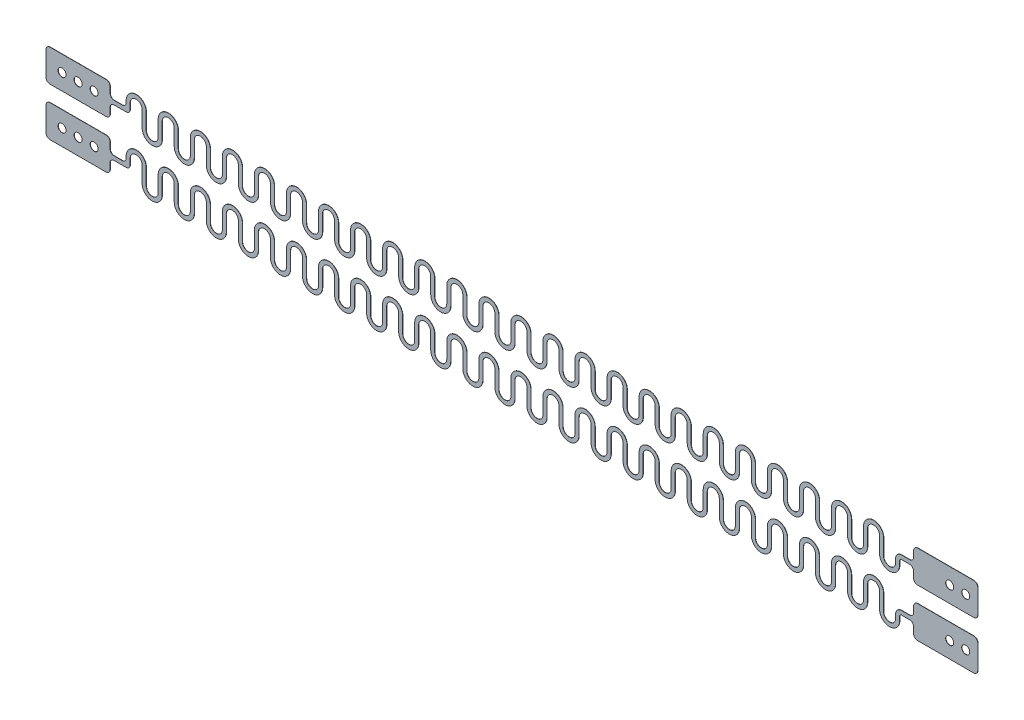
SolidWorks part; units mm, degrees
material "Copper"
ref_plane "Front Plane" through (0, 0, 0) normal (0, 0, 1) x (1, 0, 0)
ref_plane "Top Plane" through (0, 0, 0) normal (0, 1, 0) x (1, 0, 0)
ref_plane "Right Plane" through (0, 0, 0) normal (1, 0, 0) x (0, 0, -1)
sketch "Sketch1" plane through (0, 0, 0) normal (0, 0, 1) x (1, 0, 0)
  line L0 (0, -1.5) -> (0, 1.5) construction
  line L2 (-2, 0.5) -> (2, 0.5)
  line L3 (-2, 0.5) -> (-2, 2.5)
  line L4 (-2, 2.5) -> (2, 2.5)
  line L5 (2, 0.5) -> (2, 2.5)
  line L6 (-2, 0.5) -> (2, 2.5) construction
  line L7 (-2, 2.5) -> (2, 0.5) construction
  line L8 (-2, -2.5) -> (2, -2.5)
  line L9 (-2, -2.5) -> (-2, -0.5)
  line L10 (-2, -0.5) -> (2, -0.5)
  line L11 (2, -2.5) -> (2, -0.5)
  line L12 (-2, -2.5) -> (2, -0.5) construction
  line L13 (-2, -0.5) -> (2, -2.5) construction
  point P4 (0, 0)
  dimension "D1" = 2
  dimension "D2" = 4
  dimension "D3" = 2
  dimension "D5" = 3
  dimension "D12" = 4
extrude "Boss-Extrude2" add sketch "Sketch1" along normal blind 0.015
sketch "Sketch4" plane through (0, 0, 0) normal (0, 0, 1) x (1, 0, 0)
  line L0 (-2, -1.5) -> (-2.75, -1.5) construction
  line L2 (-3, -1.75) -> (-3, -2) construction
  line L3 (-3, -2) -> (-4, -2) construction
  line L4 (-4, -2) -> (-4, -1) construction
  line L5 (-4, -1) -> (-5, -1) construction
  line L22 (-5, -1) -> (-5, -1.5) construction
  line L23 (-2, -0.5) -> (-2, -2.5) construction
  line L24 (-2, -0.5) -> (-2, -2.5)
  line L25 (-2, -1.375) -> (-2.75, -1.375)
  line L30 (-3.125, -1.75) -> (-3.125, -2)
  line L31 (-3.875, -2) -> (-3.875, -1)
  line L32 (-5.125, -1) -> (-5.125, -1.5)
  line L33 (-2, -1.625) -> (-2.75, -1.625)
  line L34 (-2.875, -1.75) -> (-2.875, -2)
  line L35 (-4.125, -2) -> (-4.125, -1)
  line L36 (-4.875, -1) -> (-4.875, -1.5)
  line L37 (-5.125, -1.5) -> (-4.875, -1.5)
  arc A0 (-2.75, -1.5) -> (-3, -1.75) centre (-2.75, -1.75) ccw construction
  arc A1 (-5, -1) -> (-4, -1) centre (-4.5, -1) cw construction
  arc A2 (-4, -2) -> (-3, -2) centre (-3.5, -2) ccw construction
  arc A15 (-2.75, -1.375) -> (-3.125, -1.75) centre (-2.75, -1.75) ccw
  arc A16 (-3.875, -2) -> (-3.125, -2) centre (-3.5, -2) ccw
  arc A17 (-5.125, -1) -> (-3.875, -1) centre (-4.5, -1) cw
  arc A18 (-2.75, -1.625) -> (-2.875, -1.75) centre (-2.75, -1.75) ccw
  arc A19 (-4.125, -2) -> (-2.875, -2) centre (-3.5, -2) ccw
  arc A20 (-4.875, -1) -> (-4.125, -1) centre (-4.5, -1) cw
  point P9 (-3, -1.5)
  dimension "D5" = 1
  dimension "D7" = 0.25
  dimension "D8" = 0.5
  dimension "D9" = 0.5
  dimension "D1" = 1
  dimension "D2" = 0.5
  dimension "D3" = 1
  dimension "D4" = 1
  dimension "D6" = 0.5
  dimension "D11" = 0.125
  dimension "D10" = 0.125
extrude "Boss-Extrude4" add sketch "Sketch4" along normal blind 0.015
fillet "Fillet1" radius 0.25 6 edges at (-2, -0.5, 0.0075) (2, -0.5, 0.0075) (2, -2.5, 0.0075) (-2, -2.5, 0.0075) (-2, -1.375, 0.0075) (-2, -1.625, 0.0075)
sketch "Sketch5" plane through (0, 0, 0.015) normal (0, 0, 1) x (1, 0, 0)
  line L0 (2, -1.5) -> (1.25, -1.5) construction
  line L1 (2, -2.25) -> (2, -0.75) construction
  circle A0 centre (1.25, -1.5) radius 0.25
  circle A1 centre (0.25, -1.5) radius 0.25
  dimension "D2" = 0.5
  dimension "D1" = 0.75
  dimension "D3" = 2
extrude "Cut-Extrude1" cut sketch "Sketch5" against normal through all
sketch "Sketch7" plane through (0, 0, 0) normal (0, 0, 1) x (1, 0, 0)
  line L0 (-2, -1.5) -> (-2.75, -1.5) construction
  line L1 (-5, 2) -> (-5, 1.5)
  line L2 (-3, -1.75) -> (-3, -2) construction
  line L3 (-3, -2) -> (-4, -2) construction
  line L4 (-4, -2) -> (-4, -1) construction
  line L5 (-4, -1) -> (-5, -1) construction
  line L6 (-4.125, -2) -> (-4.125, -1)
  line L7 (-2.875, -1.75) -> (-2.875, -2)
  line L8 (-2, -1.625) -> (-2.75, -1.625)
  line L9 (-3.875, -2) -> (-3.875, -1)
  line L10 (-3.125, -1.75) -> (-3.125, -2)
  line L11 (-2, -1.375) -> (-2.75, -1.375)
  line L13 (-2, -1.625) -> (-2, -1.375)
  line L14 (-4.125, 1) -> (-4.125, 2)
  line L15 (-2.875, 1.25) -> (-2.875, 1)
  line L16 (-2, 1.375) -> (-2.75, 1.375)
  line L17 (-3.875, 1) -> (-3.875, 2)
  line L18 (-3.125, 1.25) -> (-3.125, 1)
  line L19 (-2, 1.625) -> (-2.75, 1.625)
  line L20 (-5.125, 2) -> (-4.875, 2)
  line L21 (-2, 1.5) -> (-2.75, 1.5) construction
  line L22 (-3, 1.25) -> (-3, 1) construction
  line L23 (-3, 1) -> (-4, 1) construction
  line L24 (-4, 1) -> (-4, 2) construction
  line L25 (-4, 2) -> (-5, 2) construction
  line L26 (-5.125, -1) -> (-5.125, -1.5)
  line L27 (-5.125, -1.5) -> (-4.875, -1.5)
  line L28 (-4.875, -1.5) -> (-4.875, -1)
  line L29 (-2, 1.375) -> (-2, 1.625)
  line L30 (-5, 1.5) -> (-4.875, 1.5)
  line L31 (-4.875, 1.5) -> (-4.875, 2)
  line L32 (-5.125, 2) -> (-5.125, 1.5)
  line L33 (-5.125, 1.5) -> (-5, 1.5)
  arc A0 (-3, -2) -> (-4, -2) centre (-3.5, -2) cw construction
  arc A1 (-5, -1) -> (-4, -1) centre (-4.5, -1) cw construction
  arc A2 (-2.75, -1.5) -> (-3, -1.75) centre (-2.75, -1.75) ccw construction
  arc A3 (-4.875, -1) -> (-4.125, -1) centre (-4.5, -1) cw
  arc A4 (-2.875, -2) -> (-4.125, -2) centre (-3.5, -2) cw
  arc A5 (-2.75, -1.625) -> (-2.875, -1.75) centre (-2.75, -1.75) ccw
  arc A6 (-5.125, -1) -> (-3.875, -1) centre (-4.5, -1) cw
  arc A7 (-3.125, -2) -> (-3.875, -2) centre (-3.5, -2) cw
  arc A8 (-2.75, -1.375) -> (-3.125, -1.75) centre (-2.75, -1.75) ccw
  arc A9 (-4.875, 2) -> (-4.125, 2) centre (-4.5, 2) cw
  arc A10 (-2.875, 1) -> (-4.125, 1) centre (-3.5, 1) cw
  arc A11 (-2.75, 1.375) -> (-2.875, 1.25) centre (-2.75, 1.25) ccw
  arc A12 (-5.125, 2) -> (-3.875, 2) centre (-4.5, 2) cw
  arc A13 (-3.125, 1) -> (-3.875, 1) centre (-3.5, 1) cw
  arc A14 (-2.75, 1.625) -> (-3.125, 1.25) centre (-2.75, 1.25) ccw
  arc A15 (-3, 1) -> (-4, 1) centre (-3.5, 1) cw construction
  arc A16 (-5, 2) -> (-4, 2) centre (-4.5, 2) cw construction
  arc A17 (-2.75, 1.5) -> (-3, 1.25) centre (-2.75, 1.25) ccw construction
  point P13 (-3, -1.5)
  dimension "D5" = 0.5
  dimension "D7" = 0.5
  dimension "D8" = 0.25
  dimension "D1" = 1
  dimension "D2" = 0.5
  dimension "D3" = 1
  dimension "D4" = 1
  dimension "D6" = 1
  dimension "D11" = 2
  dimension "D12" = 0.5
  dimension "D9" = 0.125
  dimension "D10" = 0.125
extrude "Boss-Extrude9" add sketch "Sketch7" along normal blind 0.015 contours L19 A14 L18 A13 L17 A12 L20 A9 L14 A10 L15 A11 L16 L29 | L32 L33 L1 L20 | L30 L31 L20 L1
fillet "Fillet2" radius 0.25 6 edges at (2, 2.5, 0.0075) (-2, 1.625, 0.0075) (-2, 2.5, 0.0075) (2, 0.5, 0.0075) (-2, 0.5, 0.0075) (-2, 1.375, 0.0075)
sketch "Sketch8" plane through (0, 0, 0.015) normal (0, 0, 1) x (1, 0, 0)
  line L0 (2, 1.5) -> (1.25, 1.5) construction
  line L1 (2, 0.75) -> (2, 2.25) construction
  circle A0 centre (1.25, 1.5) radius 0.25
  circle A1 centre (0.25, 1.5) radius 0.25
  dimension "D2" = 0.5
  dimension "D1" = 0.75
  dimension "D3" = 2
extrude "Cut-Extrude2" cut sketch "Sketch8" against normal through all
sketch "Sketch9" plane through (0, 0, 0) normal (0, 0, 1) x (1, 0, 0)
  line L2 (-5, -1.5) -> (-5, -2) construction
  line L3 (-5, -2) -> (-6, -2) construction
  line L4 (-6, -2) -> (-6, -1) construction
  line L5 (-6, -1) -> (-7, -1) construction
  line L6 (-7, -1) -> (-7, -1.5) construction
  line L7 (-5.125, -1.5) -> (-5.125, -2)
  line L8 (-5.875, -2) -> (-5.875, -1)
  line L9 (-7.125, -1) -> (-7.125, -1.5)
  line L10 (-4.875, -1.5) -> (-4.875, -2)
  line L11 (-6.125, -2) -> (-6.125, -1)
  line L12 (-6.875, -1) -> (-6.875, -1.5)
  line L13 (-7.125, -1.5) -> (-6.875, -1.5)
  line L14 (-5.125, -1.5) -> (-4.875, -1.5) construction
  line L15 (-5.125, -1.5) -> (-4.875, -1.5)
  arc A0 (-5, -2) -> (-6, -2) centre (-5.5, -2) cw construction
  arc A1 (-6, -1) -> (-7, -1) centre (-6.5, -1) ccw construction
  arc A2 (-5.125, -2) -> (-5.875, -2) centre (-5.5, -2) cw
  arc A3 (-5.875, -1) -> (-7.125, -1) centre (-6.5, -1) ccw
  arc A4 (-4.875, -2) -> (-6.125, -2) centre (-5.5, -2) cw
  arc A5 (-6.125, -1) -> (-6.875, -1) centre (-6.5, -1) ccw
  dimension "D6" = 0.5
  dimension "D7" = 0.5
  dimension "D1" = 0.5
  dimension "D2" = 1
  dimension "D3" = 1
  dimension "D4" = 1
  dimension "D5" = 0.5
  dimension "D8" = 0.125
  dimension "D9" = 0.125
extrude "Boss-Extrude10" add sketch "Sketch9" along normal up to surface (0.015 mm away) up to face at (1.5, -1.5, 0.015)
sketch "Sketch14" plane through (0, 0, 0.015) normal (0, 0, 1) x (1, 0, 0)
  line L0 (-5.125, 1.5) -> (-4.875, 1.5) construction
  line L1 (-5.125, 1.5) -> (-4.875, 1.5)
  line L2 (-5, 1.5) -> (-5, 1) construction
  line L3 (-5, 1) -> (-6, 1) construction
  line L4 (-6, 1) -> (-6, 2) construction
  line L5 (-6, 2) -> (-7, 2) construction
  line L6 (-7, 2) -> (-7, 1.5) construction
  line L7 (-5.125, 1.5) -> (-5.125, 1)
  line L8 (-5.875, 1) -> (-5.875, 2)
  line L9 (-7.125, 2) -> (-7.125, 1.5)
  line L10 (-4.875, 1.5) -> (-4.875, 1)
  line L11 (-6.125, 1) -> (-6.125, 2)
  line L12 (-6.875, 2) -> (-6.875, 1.5)
  line L13 (-7.125, 1.5) -> (-6.875, 1.5)
  arc A0 (-7, 2) -> (-6, 2) centre (-6.5, 2) cw construction
  arc A1 (-6, 1) -> (-5, 1) centre (-5.5, 1) ccw construction
  arc A2 (-5.875, 1) -> (-5.125, 1) centre (-5.5, 1) ccw
  arc A3 (-7.125, 2) -> (-5.875, 2) centre (-6.5, 2) cw
  arc A4 (-6.125, 1) -> (-4.875, 1) centre (-5.5, 1) ccw
  arc A5 (-6.875, 2) -> (-6.125, 2) centre (-6.5, 2) cw
  line M19 (-5.125, 1.5) -> (-4.875, 1.5)
  dimension "D6" = 0.5
  dimension "D7" = 0.5
  dimension "D1" = 0.5
  dimension "D2" = 1
  dimension "D3" = 1
  dimension "D4" = 1
  dimension "D5" = 0.5
  dimension "D8" = 0.125
  dimension "D9" = 0.125
extrude "Boss-Extrude16" add sketch "Sketch14" against normal up to surface (0.015 mm away) contours L12 A5 L11 A4 L10 L7 A2 L8 A3 L9 L13 M19 up to face at (1.5, 1.5, 0)
pattern_linear "LPattern3" count 23 spacing 2 along (-1, 0, 0) of "Boss-Extrude16", "Boss-Extrude10"
sketch "Sketch15" plane through (0, 0, 0.015) normal (0, 0, 1) x (1, 0, 0)
  line L0 (-51.125, -1.5) -> (-52.125, -1.5) construction
  line L1 (-51.125, -1.375) -> (-52.125, -1.375)
  line L2 (-51.125, -1.625) -> (-52.125, -1.625)
  line L3 (-50.875, -1.5) -> (-51.125, -1.5) construction
  line L4 (-50.875, -1.5) -> (-51.125, -1.5)
  line L5 (-51.125, -1.5) -> (-51.125, -1) construction
  line L6 (-51.125, -1.5) -> (-51.125, -1)
  line L7 (-51.125, -1.625) -> (-50.875, -1.625)
  line L8 (-50.875, -1.625) -> (-50.875, -1.5)
  line L10 (-56.125, -2.5) -> (-52.125, -2.5)
  line L11 (-56.125, -2.5) -> (-56.125, -0.5)
  line L12 (-56.125, -0.5) -> (-52.125, -0.5)
  line L13 (-52.125, -2.5) -> (-52.125, -0.5)
  line L14 (-56.125, -2.5) -> (-52.125, -0.5) construction
  line L15 (-56.125, -0.5) -> (-52.125, -2.5) construction
  point P11 (-54.125, -1.5)
  point P16 (-52.125, -1.5)
  dimension "D1" = 1
  dimension "D2" = 0.125
  dimension "D4" = 4
  dimension "D5" = 2
  dimension "D3" = 0.125
extrude "Boss-Extrude17" add sketch "Sketch15" against normal up to surface (0.015 mm away) contours L10 L13 L12 L11 | L13 L2 L7 L8 L4 L6 L1 up to face at (1.5, -1.5, 0)
fillet "Fillet3" radius 0.25 8 edges at (-56.125, -0.5, 0.0075) (-56.125, -2.5, 0.0075) (-52.125, -2.5, 0.0075) (-52.125, -0.5, 0.0075) (-52.125, -1.375, 0.0075) (-52.125, -1.625, 0.0075) (-50.875, -1.625, 0.0075) (-51.125, -1.375, 0.0075)
sketch "Sketch16" plane through (0, 0, 0.015) normal (0, 0, 1) x (1, 0, 0)
  line L0 (-51.125, 1.5) -> (-52.125, 1.5) construction
  line L1 (-51.125, 1.625) -> (-52.125, 1.625)
  line L2 (-51.125, 1.375) -> (-52.125, 1.375)
  line L3 (-51.125, 1.5) -> (-50.875, 1.5) construction
  line L4 (-51.125, 2) -> (-51.125, 1.5) construction
  line L5 (-51.125, 1.5) -> (-50.875, 1.5)
  line L6 (-51.125, 2) -> (-51.125, 1.5)
  line L7 (-51.125, 1.375) -> (-50.875, 1.375)
  line L8 (-50.875, 1.375) -> (-50.875, 1.5)
  line L10 (-56.125, 0.5) -> (-52.125, 0.5)
  line L11 (-56.125, 0.5) -> (-56.125, 2.5)
  line L12 (-56.125, 2.5) -> (-52.125, 2.5)
  line L13 (-52.125, 0.5) -> (-52.125, 2.5)
  line L14 (-56.125, 0.5) -> (-52.125, 2.5) construction
  line L15 (-56.125, 2.5) -> (-52.125, 0.5) construction
  point P10 (-54.125, 1.5)
  point P17 (-52.125, 1.5)
  dimension "D1" = 1
  dimension "D2" = 0.125
  dimension "D4" = 2
  dimension "D5" = 4
  dimension "D3" = 0.125
extrude "Boss-Extrude18" add sketch "Sketch16" against normal up to surface (0.015 mm away) contours L10 L13 L12 L11 | L13 L2 L7 L8 L5 L6 L1 up to face at (1.5, 1.5, 0)
fillet "Fillet4" radius 0.25 8 edges at (-56.125, 0.5, 0.0075) (-56.125, 2.5, 0.0075) (-52.125, 0.5, 0.0075) (-52.125, 2.5, 0.0075) (-52.125, 1.625, 0.0075) (-52.125, 1.375, 0.0075) (-51.125, 1.625, 0.0075) (-50.875, 1.375, 0.0075)
sketch "Sketch17" plane through (0, 0, 0.015) normal (0, 0, 1) x (1, 0, 0)
  line L0 (-56.125, 1.5) -> (-55.125, 1.5)
  line L1 (-56.125, 0.75) -> (-56.125, 2.25) construction
  circle A0 centre (-55.125, 1.5) radius 0.25
  circle A1 centre (-54.125, 1.5) radius 0.25
  circle A2 centre (-53.125, 1.5) radius 0.25
  circle A3 centre (-54.125, -1.5) radius 0.25
  circle A4 centre (-53.125, -1.5) radius 0.25
  circle A5 centre (-55.125, -1.5) radius 0.25
  dimension "D2" = 0.5
  dimension "D1" = 1
  dimension "D3" = 3
  dimension "D4" = 2
extrude "Cut-Extrude3" cut sketch "Sketch17" against normal through all
